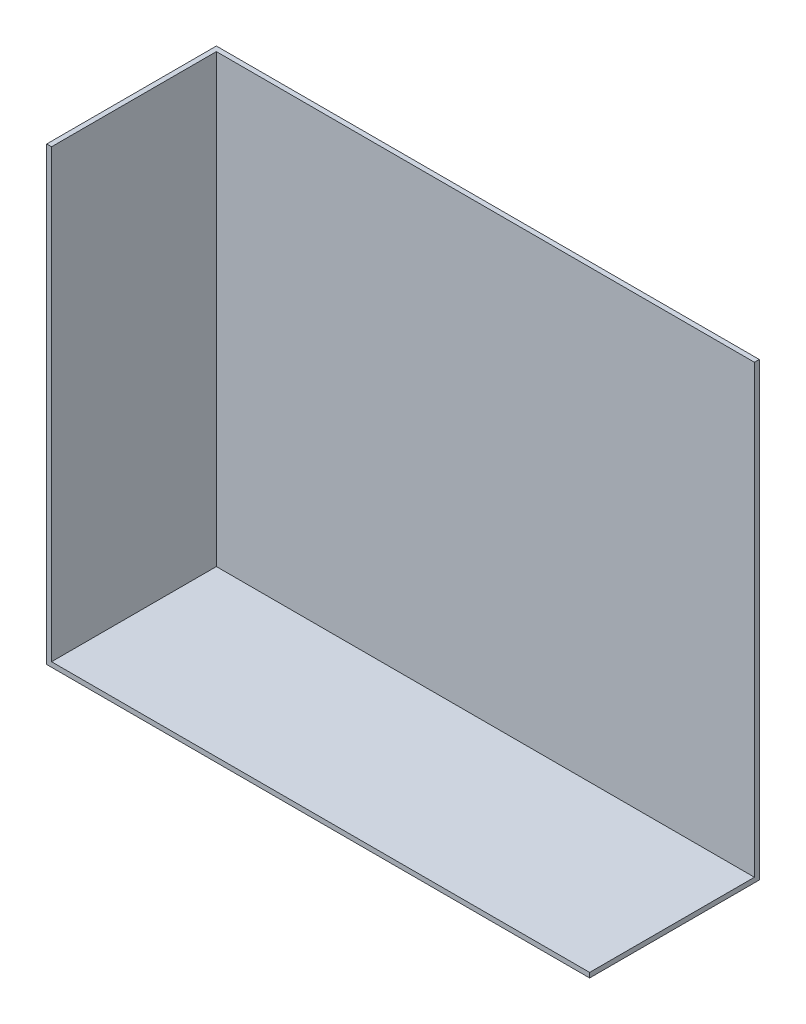
SolidWorks part; units mm, degrees
ref_plane "Front Plane" through (0, 0, 0) normal (0, 0, 1) x (1, 0, 0)
ref_plane "Top Plane" through (0, 0, 0) normal (0, 1, 0) x (1, 0, 0)
ref_plane "Right Plane" through (0, 0, 0) normal (1, 0, 0) x (0, 0, -1)
sketch "Sketch1" plane through (0, 0, 0) normal (0, 1, 0) x (1, 0, 0)
  line L1 (1422.4, 444.5) -> (-1422.4, 444.5)
  line L2 (1422.4, 444.5) -> (1422.4, -444.5)
  line L3 (1422.4, -444.5) -> (-1422.4, -444.5)
  line L4 (-1422.4, 444.5) -> (-1422.4, -444.5)
  line L5 (1422.4, 444.5) -> (-1422.4, -444.5) construction
  line L6 (1422.4, -444.5) -> (-1422.4, 444.5) construction
  point P0 (0, 0)
  dimension "D1" = 2844.8
  dimension "D2" = 889
extrude "Boss-Extrude1" add sketch "Sketch1" along normal blind 2362.2
shell "Shell1" thickness 25.4
